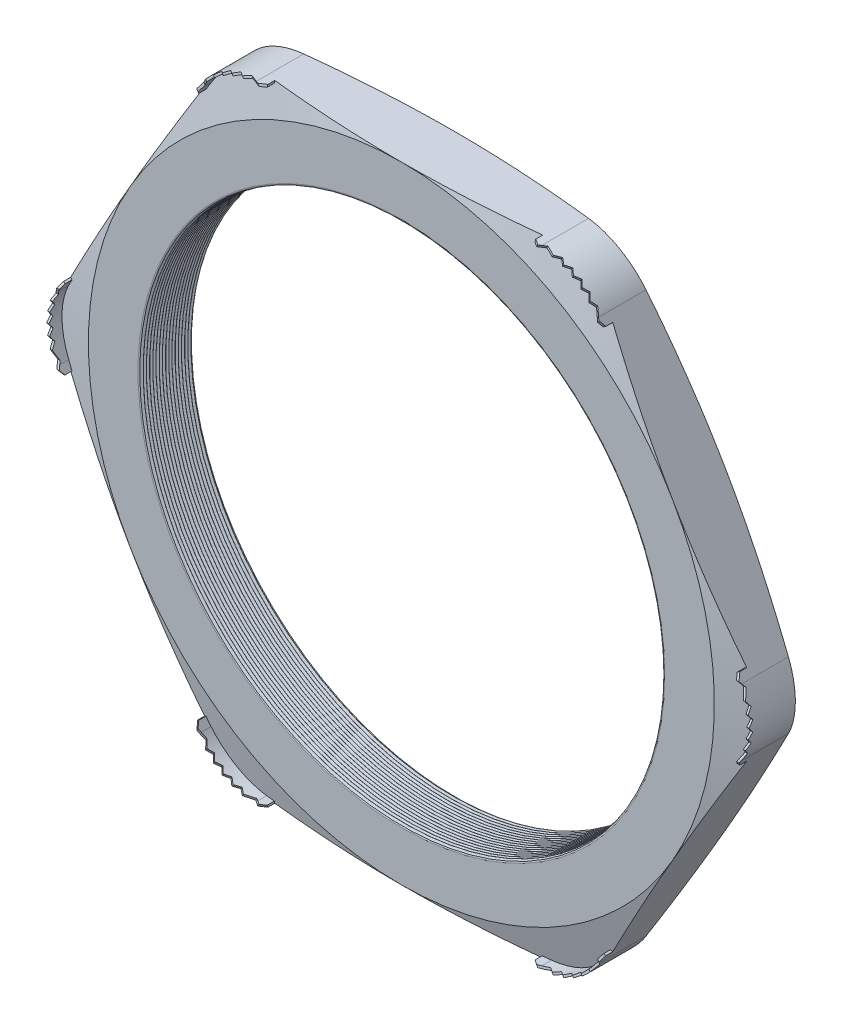
SolidWorks part; units mm, degrees
ref_plane "Front Plane" through (0, 0, 0) normal (0, 0, 1) x (1, 0, 0)
ref_plane "Top Plane" through (0, 0, 0) normal (0, 1, 0) x (1, 0, 0)
ref_plane "Right Plane" through (0, 0, 0) normal (1, 0, 0) x (0, 0, -1)
sketch "Sketch1" plane through (0, 0, 0) normal (0, 0, 1) x (1, 0, 0)
  line L1 (-34.6087, 0) -> (-17.3043, -29.972)
  line L2 (-17.3043, -29.972) -> (17.3043, -29.972)
  line L3 (17.3043, -29.972) -> (34.6087, 0)
  line L4 (34.6087, 0) -> (17.3043, 29.972)
  line L5 (17.3043, 29.972) -> (-17.3043, 29.972)
  line L6 (-17.3043, 29.972) -> (-34.6087, 0)
  circle A0 centre (0, 0) radius 29.972 construction
  circle A1 centre (0, 0) radius 25.019
  dimension "TS" = 50.038
  dimension "H" = 59.944
extrude "Extrude1" add sketch "Sketch1" along normal blind 5.08
fillet "Fillet1" radius 6.35 6 edges at (-17.3043, 29.972, 2.54) (-34.6087, 0, 2.54) (-17.3043, -29.972, 2.54) (17.3043, -29.972, 2.54) (34.6087, 0, 2.54) (17.3043, 29.972, 2.54)
sketch "Sketch2" plane through (0, 0, 5.08) normal (0, 0, 1) x (1, 0, 0)
  line L0 (-13.6382, 29.972) -> (-12.8254, 29.972)
  line L1 (13.6382, 29.972) -> (-13.6382, 29.972) construction
  line L2 (-19.1374, 26.797) -> (-19.5438, 26.0931)
  line L3 (-19.1374, 26.797) -> (-32.7756, 3.175) construction
  line L4 (-13.6382, 29.7688) -> (-12.8254, 29.7688)
  line L5 (-18.9615, 26.6954) -> (-19.3679, 25.9915)
  line L6 (-19.5438, 26.0931) -> (-19.3679, 25.9915)
  line L7 (-12.8254, 29.972) -> (-12.8254, 29.7688)
  arc A0 (-13.6382, 29.7688) -> (-18.9615, 26.6954) centre (-13.6382, 23.622) ccw
  arc A1 (-13.6382, 29.972) -> (-19.1374, 26.797) centre (-13.6382, 23.622) ccw construction
  arc A4 (-13.6382, 29.972) -> (-19.1374, 26.797) centre (-13.6382, 23.622) ccw
  dimension "D1" = 0.8128
  dimension "D2" = 0.8128
  dimension "OFFSET" = 0.2032
fillet "Fillet3" radius 0.2032 2 edges at (25.019, 0, 0) (25.019, 0, 5.08)
sketch "Sketch3" plane through (0, 0, 0) normal (0, 1, 0) x (1, 0, 0)
  line L0 (-25.019, -5.08) -> (-25.019, -4.7867)
  line L2 (-25.019, -4.7867) -> (-25.273, -4.9334)
  line L3 (-25.273, -4.9334) -> (-25.019, -5.08)
  line L4 (-25.019, -0.2032) -> (-25.019, -4.8768) construction
  line L5 (-19.1374, -5.08) -> (-32.7756, -5.08) construction
  dimension "D1" = 60
  dimension "D2" = 60
  dimension "D3" = 0.254
revolve "Cut-Revolve1" cut sketch "Sketch3" angle 360 about axis through (0, 0, 5.08) along (0, 0, -1)
pattern_linear "LPattern1" count 17 spacing 0.3048 along (0, 0, -1) of "Cut-Revolve1"
sketch "Sketch4" plane through (0, 0, 0) normal (0, 0, -1) x (-1, 0, 0)
  line L0 (-32.7756, 3.175) -> (-19.1374, 26.797) construction
  circle A0 centre (0, 0) radius 29.972
extrude "Cut-Extrude1" cut sketch "Sketch4" against normal through all draft 75 flip side to cut
sketch "Sketch5" plane through (0, 0, 5.08) normal (0, 0, 1) x (1, 0, 0)
  line L0 (13.6382, 29.972) -> (-13.6382, 29.972) construction
  circle A0 centre (0, 0) radius 29.972
extrude "Cut-Extrude2" cut sketch "Sketch5" against normal through all draft 75 flip side to cut
extrude "Extrude2" add sketch "Sketch2" along normal blind 0.9144 and the other way up to next
ref_plane "Plane1" through (-16.0966, 27.8801, 0) normal (0.5, -0.866, 0) x (0.866, 0.5, 0)
sketch "Sketch7" plane through (-16.0966, 27.8801, 0) normal (0.5, -0.866, 0) x (0.866, 0.5, 0)
  line L0 (-3.8789, 5.0343) -> (-3.3709, 5.4183)
  line L1 (-3.8789, 4.3756) -> (-3.8789, 5.9944) construction
  line L2 (0, 1.3136) -> (0, 4.0135) construction
  line L4 (-3.3709, 5.4183) -> (-2.8629, 5.0343)
  line L5 (-1.016, 5.4183) -> (-0.508, 5.0343)
  line L6 (-2.032, 5.4183) -> (-1.524, 5.0343)
  line L7 (-0.508, 5.0343) -> (0, 5.4183)
  line L8 (0, 5.4183) -> (0.508, 5.0343)
  line L10 (1.016, 5.4183) -> (1.524, 5.0343)
  line L11 (2.032, 5.4183) -> (2.54, 5.0343)
  line L12 (-2.8629, 5.0343) -> (-2.032, 5.4183)
  line L13 (-1.524, 5.0343) -> (-1.016, 5.4183)
  line L14 (0.508, 5.0343) -> (1.016, 5.4183)
  line L15 (3.3709, 5.4183) -> (3.8789, 5.0343)
  line L16 (3.8789, 4.3756) -> (3.8789, 5.9944) construction
  line L17 (-3.8789, 5.0343) -> (-3.8789, 5.9944)
  line L19 (-3.8789, 5.9944) -> (3.8789, 5.9944)
  line L20 (3.8789, 5.9944) -> (3.8789, 5.0343)
  line L23 (1.524, 5.0343) -> (2.032, 5.4183)
  line L25 (2.54, 5.0343) -> (3.3709, 5.4183)
  dimension "D1" = 0.9601
  dimension "D2" = 0.5761
  dimension "D3" = 0.508
extrude "Cut-Extrude4" cut sketch "Sketch7" against normal through all
pattern_circular "CirPattern1" count 6 over 360 about axis through (0, 0, 0) along (0, 0, 1) of "Extrude2"
pattern_circular "CirPattern2" count 6 over 360 about axis through (0, 0, 0) along (0, 0, 1) of "Cut-Extrude4"
